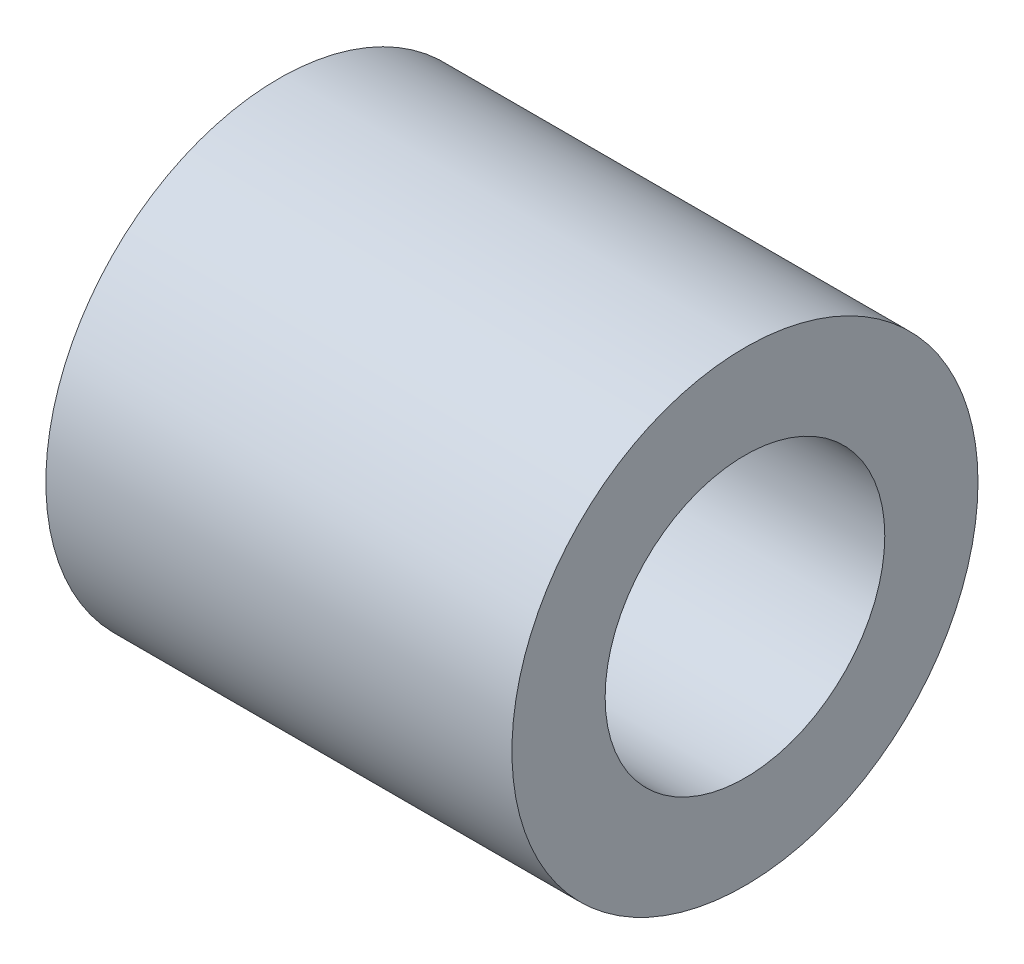
SolidWorks part; units mm, degrees
ref_plane "Front" through (0, 0, 0) normal (0, 0, 1) x (1, 0, 0)
ref_plane "Top" through (0, 0, 0) normal (0, 1, 0) x (1, 0, 0)
ref_plane "Right" through (0, 0, 0) normal (1, 0, 0) x (0, 0, -1)
sketch "Sketch1" plane through (0, 0, 0) normal (1, 0, 0) x (0, 0, -1)
  circle A0 centre (0, 0) radius 1.5
  circle A1 centre (0, 0) radius 2.5
  dimension "D1" = 3
  dimension "D2" = 5
extrude "Boss-Extrude1" add sketch "Sketch1" along normal mid plane 5
